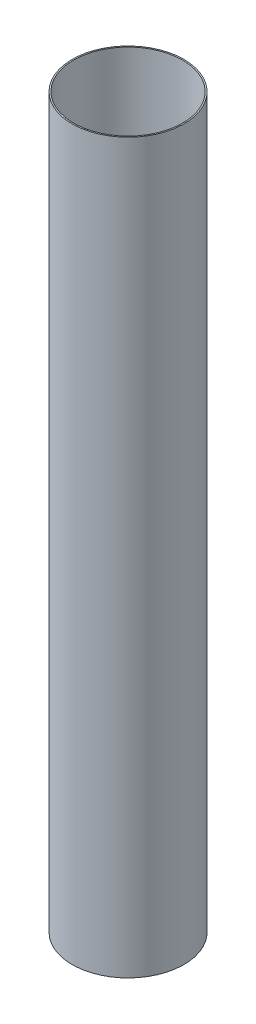
SolidWorks part; units mm, degrees
ref_plane "Front Plane" through (0, 0, 0) normal (0, 0, 1) x (1, 0, 0)
ref_plane "Top Plane" through (0, 0, 0) normal (0, 1, 0) x (1, 0, 0)
ref_plane "Right Plane" through (0, 0, 0) normal (1, 0, 0) x (0, 0, -1)
sketch "Sketch1" plane through (0, 0, 0) normal (0, 0, 1) x (1, 0, 0)
  line L1 (19.0373, 0) -> (19.4945, 0)
  line L2 (19.0373, 0) -> (19.0373, 254)
  line L3 (19.0373, 254) -> (19.4945, 254)
  line L4 (19.4945, 0) -> (19.4945, 254)
  dimension "D1" = 19.4945
  dimension "D2" = 0.4572
  dimension "D3" = 254
  dimension "D4" = 0
ref_axis "Axis1" through (0, -13.97, 0) along (0, 1, 0)
revolve "Revolve1" add sketch "Sketch1" angle 360 about axis through (0, -13.97, 0) along (0, 1, 0)
